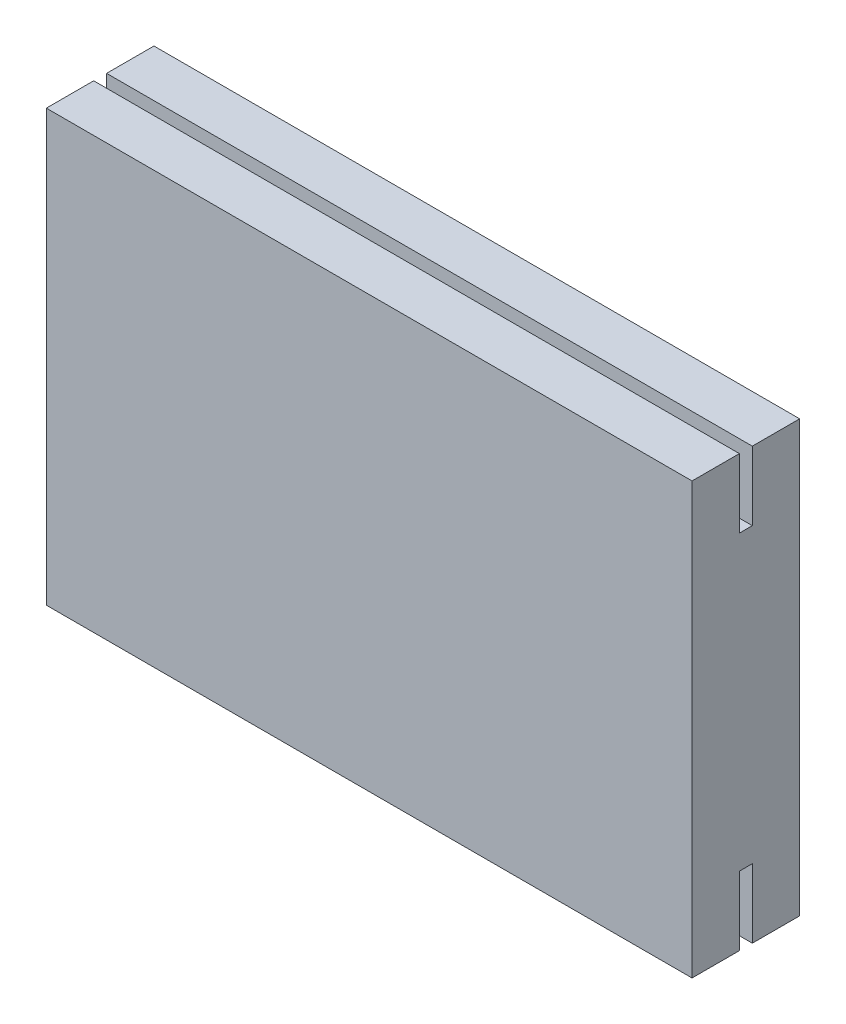
SolidWorks part; units mm, degrees
material "ABS"
ref_plane "Front Plane" through (0, 0, 0) normal (0, 0, 1) x (1, 0, 0)
ref_plane "Top Plane" through (0, 0, 0) normal (0, 1, 0) x (1, 0, 0)
ref_plane "Right Plane" through (0, 0, 0) normal (1, 0, 0) x (0, 0, -1)
sketch "Sketch4" plane through (0, 0, 0) normal (1, 0, 0) x (0, 0, -1)
  line L1 (2.5, -10) -> (-2.5, -10)
  line L2 (2.5, -10) -> (2.5, 10)
  line L3 (2.5, 10) -> (-2.5, 10)
  line L4 (-2.5, -10) -> (-2.5, 10)
  line L5 (2.5, -10) -> (-2.5, 10) construction
  line L6 (2.5, 10) -> (-2.5, -10) construction
  point P0 (0, 0)
  dimension "D1" = 5
  dimension "D2" = 20
extrude "Boss-Extrude2" add sketch "Sketch4" along normal blind 30
sketch "Sketch5" plane through (30, 0, 0) normal (1, 0, 0) x (0, 0, -1)
  line L0 (0, 10) -> (0, 0) construction
  line L1 (2.5, 10) -> (-2.5, 10) construction
  line L2 (2.5, 10) -> (-2.5, 10)
  line L3 (0, 10) -> (-0.3, 10)
  line L4 (-0.3, 10) -> (-0.3, 6.8)
  line L5 (-0.3, 6.8) -> (0.3, 6.8)
  line L6 (0.3, 10) -> (0.3, 6.8)
  point P9 (0, 6.8)
  dimension "D1" = 3.2
  dimension "D2" = 0.3
extrude "Cut-Extrude3" cut sketch "Sketch5" against normal through all contours L0 L2 L4 L5 | L2 L0 L5 L6
mirror "Mirror3" about plane through (0, 0, 0) normal (0, 1, 0) of "Cut-Extrude3"
